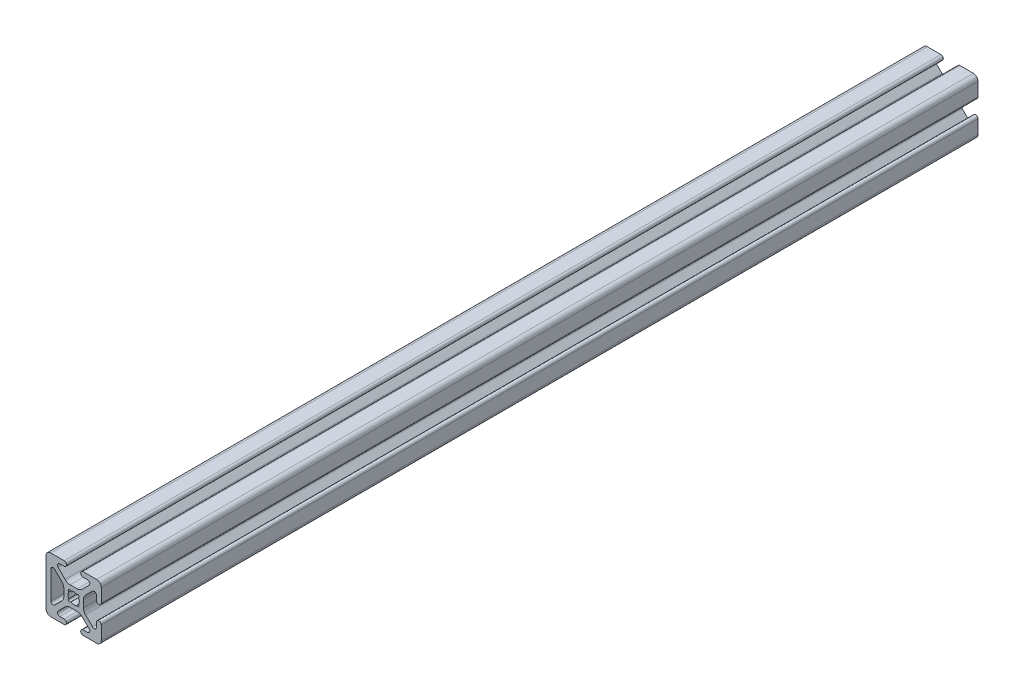
SolidWorks part; units mm, degrees
ref_plane "Front Plane" through (0, 0, 0) normal (0, 0, 1) x (1, 0, 0)
ref_plane "Top Plane" through (0, 0, 0) normal (0, 1, 0) x (1, 0, 0)
ref_plane "Right Plane" through (0, 0, 0) normal (1, 0, 0) x (0, 0, -1)
ref_plane "Plane1" through (0, 0, 12.7) normal (0, 0, 1) x (1, 0, 0)
sketch "Sketch1" plane through (0, 0, 12.7) normal (0, 0, 1) x (1, 0, 0)
  line L0 (-8.6817, 7.1192) -> (-5.4471, 3.8846)
  line L1 (-4.5172, 1.6396) -> (-4.5172, -1.6396)
  line L2 (-5.4471, -3.8846) -> (-8.6817, -7.1192)
  line L3 (-10.4902, -6.3701) -> (-10.4902, 6.3701)
  line L4 (-12.7, 10.5918) -> (-12.7, -10.5918)
  line L5 (-10.5918, -12.7) -> (-4.3561, -12.7)
  line L6 (-4.3561, -10.4902) -> (-6.3701, -10.4902)
  line L7 (-7.1192, -8.6817) -> (-3.8846, -5.4471)
  line L8 (-1.6396, -4.5172) -> (1.6396, -4.5172)
  line L9 (3.8846, -5.4471) -> (7.1192, -8.6817)
  line L10 (6.3701, -10.4902) -> (4.3561, -10.4902)
  line L11 (4.3561, -12.7) -> (10.5918, -12.7)
  line L12 (12.7, -10.5918) -> (12.7, -4.3561)
  line L13 (10.4902, -4.3561) -> (10.4902, -6.3701)
  line L14 (8.6817, -7.1192) -> (5.4471, -3.8846)
  line L15 (4.5172, -1.6396) -> (4.5172, 1.6396)
  line L16 (5.4471, 3.8846) -> (8.6817, 7.1192)
  line L17 (10.4902, 6.3701) -> (10.4902, 4.3561)
  line L18 (12.7, 4.3561) -> (12.7, 10.5918)
  line L19 (10.5918, 12.7) -> (4.3561, 12.7)
  line L20 (4.3561, 10.4902) -> (6.3701, 10.4902)
  line L21 (7.1192, 8.6817) -> (3.8846, 5.4471)
  line L22 (1.6396, 4.5172) -> (-1.6396, 4.5172)
  line L23 (-3.8846, 5.4471) -> (-7.1192, 8.6817)
  line L24 (-6.3701, 10.4902) -> (-4.3561, 10.4902)
  line L25 (-4.3561, 12.7) -> (-10.5918, 12.7)
  arc A0 (-10.4902, 6.3701) -> (-8.6817, 7.1192) centre (-9.4308, 6.3701) cw
  arc A1 (-5.4471, 3.8846) -> (-4.5172, 1.6396) centre (-7.6922, 1.6396) cw
  arc A2 (-4.5172, -1.6396) -> (-5.4471, -3.8846) centre (-7.6922, -1.6396) cw
  arc A3 (-8.6817, -7.1192) -> (-10.4902, -6.3701) centre (-9.4308, -6.3701) cw
  arc A4 (-2.2319, 1.3405) -> (-1.3405, 2.2319) centre (-1.841, 1.841) cw
  arc A5 (-1.3405, 2.2319) -> (1.3405, 2.2319) centre (0, 0) cw
  arc A6 (1.3405, 2.2319) -> (2.2319, 1.3405) centre (1.841, 1.841) cw
  arc A7 (2.2319, 1.3405) -> (2.2319, -1.3405) centre (0, 0) cw
  arc A8 (2.2319, -1.3405) -> (1.3405, -2.2319) centre (1.841, -1.841) cw
  arc A9 (1.3405, -2.2319) -> (-1.3405, -2.2319) centre (0, 0) cw
  arc A10 (-1.3405, -2.2319) -> (-2.2319, -1.3405) centre (-1.841, -1.841) cw
  arc A11 (-2.2319, -1.3405) -> (-2.2319, 1.3405) centre (0, 0) cw
  arc A12 (-10.5918, 12.7) -> (-12.7, 10.5918) centre (-10.5918, 10.5918) ccw
  arc A13 (-12.7, -10.5918) -> (-10.5918, -12.7) centre (-10.5918, -10.5918) ccw
  arc A14 (-4.3561, -12.7) -> (-4.3561, -10.4902) centre (-4.3561, -11.5951) ccw
  arc A15 (-6.3701, -10.4902) -> (-7.1192, -8.6817) centre (-6.3701, -9.4308) cw
  arc A16 (-3.8846, -5.4471) -> (-1.6396, -4.5172) centre (-1.6396, -7.6922) cw
  arc A17 (1.6396, -4.5172) -> (3.8846, -5.4471) centre (1.6396, -7.6922) cw
  arc A18 (7.1192, -8.6817) -> (6.3701, -10.4902) centre (6.3701, -9.4308) cw
  arc A19 (4.3561, -10.4902) -> (4.3561, -12.7) centre (4.3561, -11.5951) ccw
  arc A20 (10.5918, -12.7) -> (12.7, -10.5918) centre (10.5918, -10.5918) ccw
  arc A21 (12.7, -4.3561) -> (10.4902, -4.3561) centre (11.5951, -4.3561) ccw
  arc A22 (10.4902, -6.3701) -> (8.6817, -7.1192) centre (9.4308, -6.3701) cw
  arc A23 (5.4471, -3.8846) -> (4.5172, -1.6396) centre (7.6922, -1.6396) cw
  arc A24 (4.5172, 1.6396) -> (5.4471, 3.8846) centre (7.6922, 1.6396) cw
  arc A25 (8.6817, 7.1192) -> (10.4902, 6.3701) centre (9.4308, 6.3701) cw
  arc A26 (10.4902, 4.3561) -> (12.7, 4.3561) centre (11.5951, 4.3561) ccw
  arc A27 (12.7, 10.5918) -> (10.5918, 12.7) centre (10.5918, 10.5918) ccw
  arc A28 (4.3561, 12.7) -> (4.3561, 10.4902) centre (4.3561, 11.5951) ccw
  arc A29 (6.3701, 10.4902) -> (7.1192, 8.6817) centre (6.3701, 9.4308) cw
  arc A30 (3.8846, 5.4471) -> (1.6396, 4.5172) centre (1.6396, 7.6922) cw
  arc A31 (-1.6396, 4.5172) -> (-3.8846, 5.4471) centre (-1.6396, 7.6922) cw
  arc A32 (-7.1192, 8.6817) -> (-6.3701, 10.4902) centre (-6.3701, 9.4308) cw
  arc A33 (-4.3561, 10.4902) -> (-4.3561, 12.7) centre (-4.3561, 11.5951) ccw
extrude "Boss-Extrude1" add sketch "Sketch1" against normal blind 403
hole_wizard "1/4-20 Tapped Hole1" positions "3DSketch2" profile "Sketch5" tap size "1/4-20" standard "ANSI Inch"
sketch3d "3DSketch2"
  line L0 (-1.6396, 4.5172, -390.3) -> (-1.6396, 4.5172, 12.7) construction
  line L1 (1.6396, 4.5172, -390.3) -> (1.6396, 4.5172, 12.7) construction
  line L2 (-1.6396, 4.5172, -390.3) -> (-1.6396, 4.5172, 12.7) construction
  line L3 (1.6396, 4.5172, -390.3) -> (1.6396, 4.5172, 12.7) construction
  line L4 (1.6396, 4.5172, -40.35) -> (-1.6396, 4.5172, -40.35) construction
  point P8 (0, 4.5172, -40.35)
  point P10 (0, 4.5172, -40.35)
  dimension "D1" = 53.05
cosmetic thread "Hole Thread3" parameters "D1"=9.1685, "D2"=6.35
cosmetic thread "Hole Thread4" parameters "D1"=9.1685, "D2"=6.35
sketch "Sketch5" plane through (0, 4.5172, -40.35) normal (1, 0, 0) x (0, 0, 1)
  line L0 (0, 0) -> (0, 18.75)
  line L1 (0, 18.75) -> (2.5527, 17.2162)
  line L2 (2.5527, 17.2162) -> (2.5527, 0)
  line L5 (2.5527, 0) -> (0, 0)
  line L10 (0, 18.75) -> (-2.5527, 17.2162) construction
  line L11 (0, -6.35) -> (0, 107.95) construction
  dimension "Tap Drill Dia." = 5.1054
  dimension "Tap Drill Depth" = 17.2162
  dimension "Drill Angle" = 118
